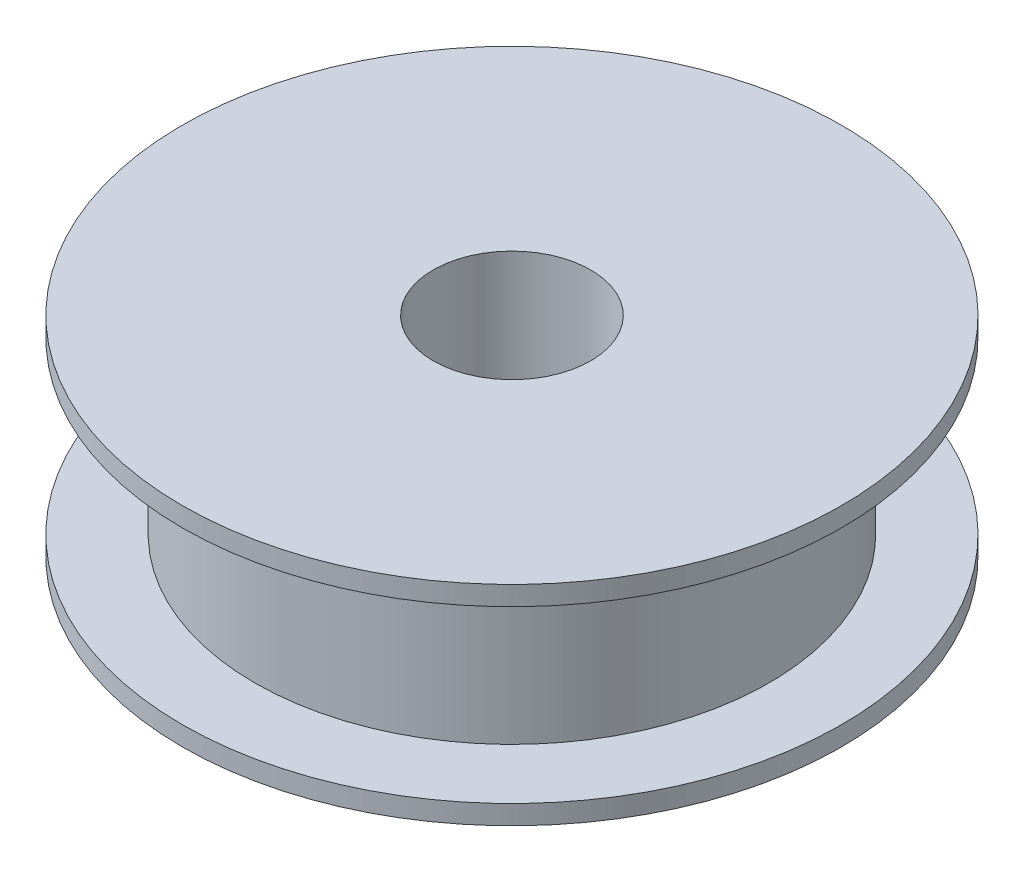
SolidWorks part; units mm, degrees
ref_plane "Plano frontal" through (0, 0, 0) normal (0, 0, 1) x (1, 0, 0)
ref_plane "Plano superior" through (0, 0, 0) normal (0, 1, 0) x (1, 0, 0)
ref_plane "Plano direito" through (0, 0, 0) normal (1, 0, 0) x (0, 0, -1)
sketch "Esboço1" plane through (0, 0, 0) normal (0, 0, 1) x (1, 0, 0)
  line L0 (0, 29.9893) -> (0, 0) construction
  line L1 (24.5, 0) -> (102.5, 0)
  line L2 (102.5, 0) -> (102.5, 6)
  line L3 (102.5, 6) -> (80, 6)
  line L4 (80, 6) -> (80, 59)
  line L5 (24.5, 0) -> (24.5, 65)
  line L6 (0, 32.5) -> (80, 32.5) construction
  line L7 (102.5, 59) -> (80, 59)
  line L8 (102.5, 65) -> (102.5, 59)
  line L9 (24.5, 65) -> (102.5, 65)
  point P10 (24.5, 32.5)
  point P12 (24.5, 32.5)
  dimension "D1" = 49
  dimension "D2" = 205
  dimension "D3" = 160
  dimension "D4" = 6
  dimension "D5" = 65
revolve "Revolução1" add sketch "Esboço1" angle 360 about L0
